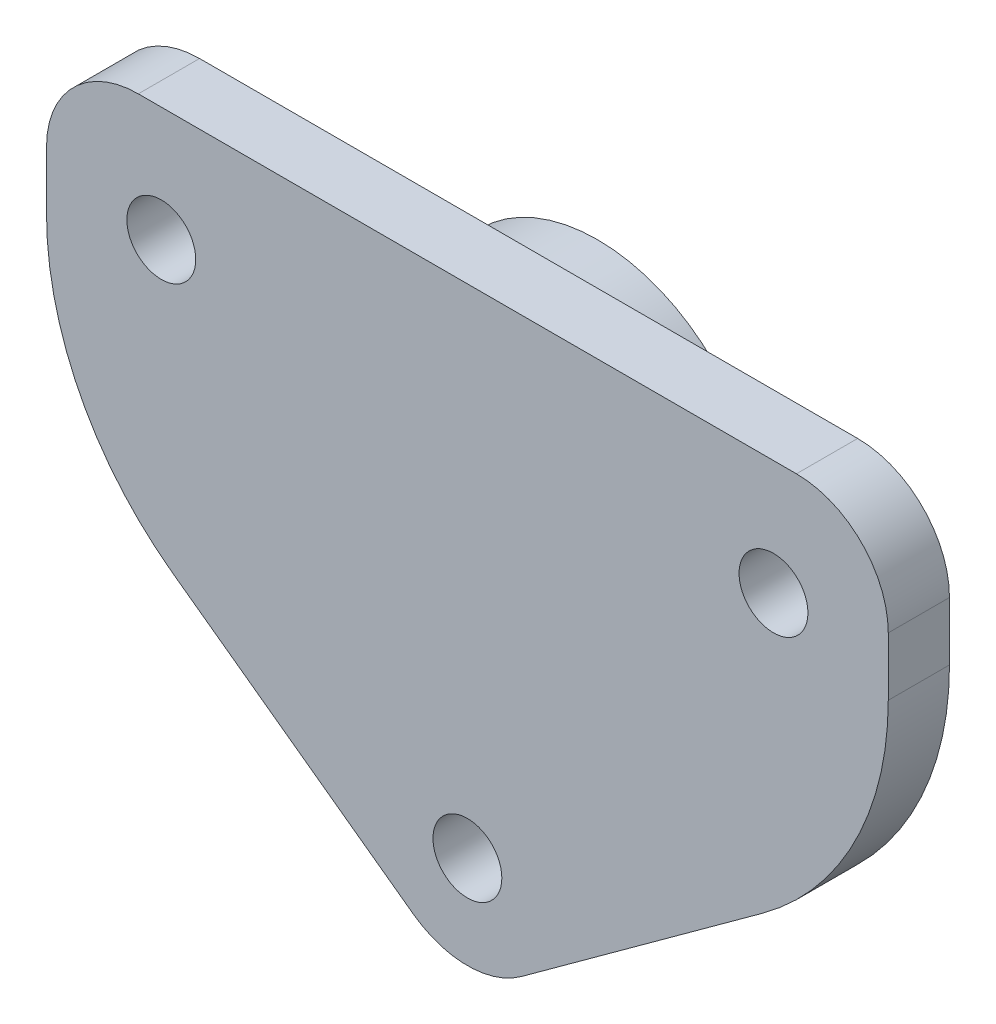
SolidWorks part; units mm, degrees
ref_plane "Plan de face" through (0, 0, 0) normal (0, 0, 1) x (1, 0, 0)
ref_plane "Plan de dessus" through (0, 0, 0) normal (0, 1, 0) x (1, 0, 0)
ref_plane "Plan de droite" through (0, 0, 0) normal (1, 0, 0) x (0, 0, -1)
sketch "Esquisse1" plane through (0, 0, 0) normal (0, 0, 1) x (1, 0, 0)
  line L0 (-55, 20) -> (-27.5, 0)
  line L1 (-55, 40) -> (0, 40)
  line L2 (-55, 40) -> (-55, 20)
  line L4 (0, 40) -> (0, 20)
  line L5 (-27.5, 0) -> (0, 20)
  circle A1 centre (-47.5, 32.5) radius 2.25
  circle A2 centre (-7.5, 32.5) radius 2.25
  circle A3 centre (-27.5, 7.5) radius 2.25
  dimension "D3" = 4.5
  dimension "D4" = 4.5
  dimension "D5" = 4.5
  dimension "D12" = 7.5
  dimension "D13" = 7.5
  dimension "D14" = 7.5
  dimension "D15" = 7.5
  dimension "D1" = 55
  dimension "D2" = 40
extrude "Boss.-Extru.1" add sketch "Esquisse1" along normal blind 4
fillet "Congé2" radius 6 3 edges at (-27.5, 0, 2) (-55, 40, 2) (0, 40, 2)
fillet "Congé3" radius 20 2 edges at (-55, 20, 2) (0, 20, 2)
sketch "Esquisse2" plane through (0, 0, 0) normal (0, 0, -1) x (-1, 0, 0)
  line L0 (0, 30.1845) -> (0, 34) construction
  line L1 (55, 34) -> (55, 30.1845) construction
  circle A0 centre (27.5, 27.5) radius 10.75
  arc A1 (23.971, 2.5666) -> (31.029, 2.5666) centre (27.5, 7.419) ccw construction
  circle A2 centre (27.5, 7.5) radius 2.25 construction
  point P6 (27.5, 1.419)
  dimension "D1" = 21.5
  dimension "D2" = 27.5
  dimension "D3" = 27.5
  dimension "D4" = 20
extrude "Boss.-Extru.2" add sketch "Esquisse2" along normal blind 4.5
